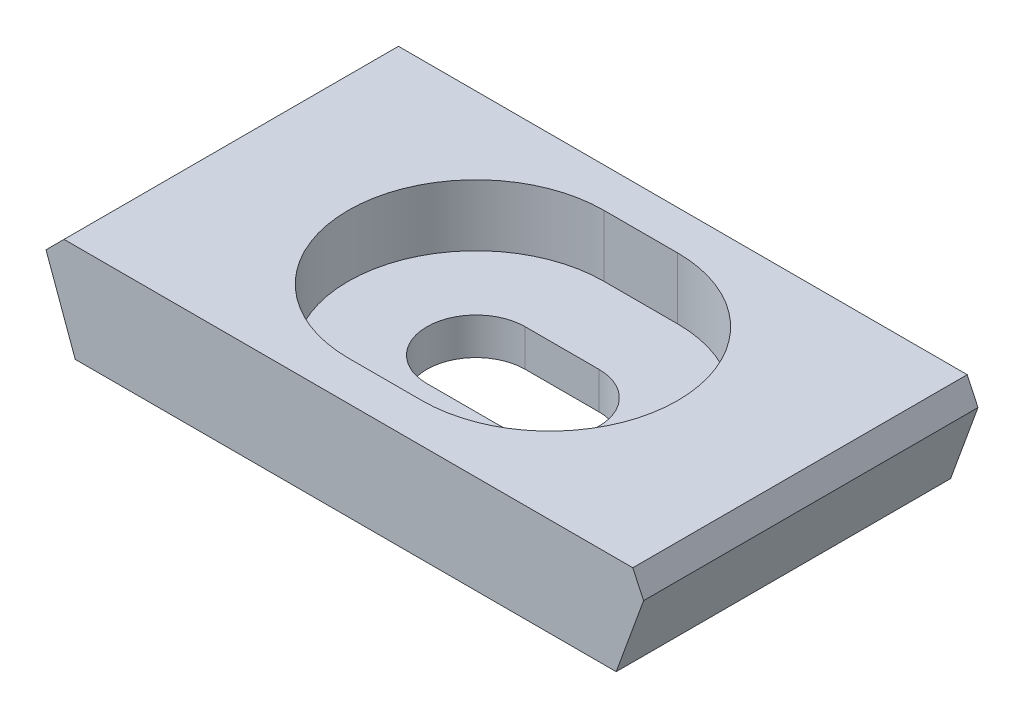
SolidWorks part; units mm, degrees
ref_plane "Front Plane" through (0, 0, 0) normal (0, 0, 1) x (1, 0, 0)
ref_plane "Top Plane" through (0, 0, 0) normal (0, 1, 0) x (1, 0, 0)
ref_plane "Right Plane" through (0, 0, 0) normal (1, 0, 0) x (0, 0, -1)
sketch "Sketch1" plane through (0, 0, 0) normal (0, 0, 1) x (1, 0, 0)
  line L0 (-13.97, 0) -> (13.97, 0)
  line L1 (13.97, 0) -> (15.819, 5.08)
  line L2 (15.819, 5.08) -> (-15.819, 5.08)
  line L3 (-15.819, 5.08) -> (-13.97, 0)
  dimension "D1" = 27.94
  dimension "D2" = 70
  dimension "D3" = 70
  dimension "D4" = 5.08
  dimension "D5" = 13.97
extrude "Boss-Extrude1" add sketch "Sketch1" along normal blind 17.272
sketch "Sketch2" plane through (0, 5.08, 0) normal (0, 1, 0) x (1, 0, 0)
  line L0 (1.905, -8.636) -> (-1.905, -8.636) construction
  line L1 (1.905, -15.24) -> (-1.905, -15.24)
  line L2 (1.905, -2.032) -> (-1.905, -2.032)
  line L4 (15.819, 0) -> (-15.819, 0)
  line L5 (-15.819, 0) -> (-15.819, -17.272)
  line L6 (-15.819, -17.272) -> (15.819, -17.272)
  line L7 (15.819, -17.272) -> (15.819, 0)
  line L8 (15.819, 0) -> (-15.819, 0)
  line L9 (-15.819, 0) -> (-15.819, -17.272)
  line L10 (-15.819, -17.272) -> (15.819, -17.272)
  line L11 (15.819, -17.272) -> (15.819, 0)
  arc A1 (1.905, -15.24) -> (1.905, -2.032) centre (1.905, -8.636) ccw
  arc A2 (-1.905, -2.032) -> (-1.905, -15.24) centre (-1.905, -8.636) ccw
  point P4 (0, -8.636)
  point P12 (0, 0)
  point P13 (0, 0)
  point P14 (0, 0)
  dimension "D2" = 17.272
  dimension "D4" = 31.6379
  dimension "D3" = 13.208
  dimension "D5" = 3.81
  dimension "D6" = 8.636
  dimension "D7" = 15.819
  dimension "D1" = 0
extrude "Cut-Extrude1" cut sketch "Sketch2" against normal blind 3.175 flip side to cut
sketch "Sketch4" plane through (0, 1.905, 0) normal (0, 1, 0) x (1, 0, 0)
  line L0 (1.905, -8.636) -> (-1.905, -8.636) construction
  line L1 (1.905, -11.176) -> (-1.905, -11.176)
  line L2 (1.905, -6.096) -> (-1.905, -6.096)
  arc A0 (1.905, -11.176) -> (1.905, -6.096) centre (1.905, -8.636) ccw
  arc A1 (-1.905, -6.096) -> (-1.905, -11.176) centre (-1.905, -8.636) ccw
  arc A2 (-1.905, -2.032) -> (-1.905, -15.24) centre (-1.905, -8.636) ccw construction
  arc A3 (1.905, -15.24) -> (1.905, -2.032) centre (1.905, -8.636) ccw construction
  point P2 (0, -8.636)
  dimension "D1" = 2.54
extrude "Cut-Extrude3" cut sketch "Sketch4" against normal through all
chamfer "Chamfer1" distance 1.27 angle 45 4 edges at (-15.819, 5.08, 8.636) (15.819, 5.08, 8.636) (0, 5.08, 0) (0, 5.08, 17.272)
equation "\"D5@Sketch1\"=\"D1@Sketch1\"/2"
equation "\"D6@Sketch2\"=\"D2@Sketch2\"/2"
equation "\"D7@Sketch2\"=\"D4@Sketch2\"/2"
